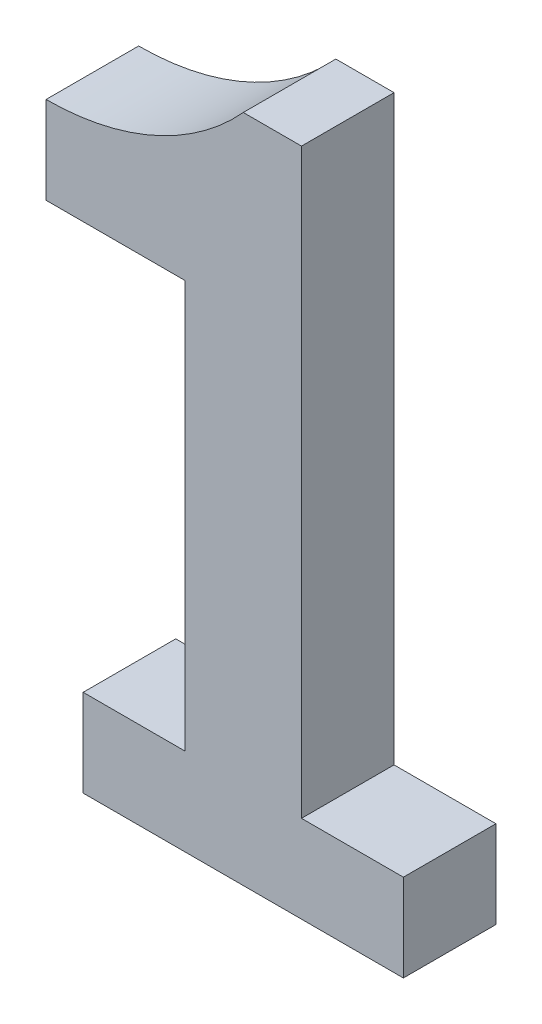
SolidWorks part; units mm, degrees
ref_plane "Front Plane" through (0, 0, 0) normal (0, 0, 1) x (1, 0, 0)
ref_plane "Top Plane" through (0, 0, 0) normal (0, 1, 0) x (1, 0, 0)
ref_plane "Right Plane" through (0, 0, 0) normal (1, 0, 0) x (0, 0, -1)
sketch "Sketch1" plane through (0, 0, 0) normal (0, 0, 1) x (1, 0, 0)
  line L1 (-76.2, 57.15) -> (76.2, 57.15)
  line L2 (-76.2, 57.15) -> (-76.2, -57.15)
  line L3 (-76.2, -57.15) -> (76.2, -57.15)
  line L4 (76.2, 57.15) -> (76.2, -57.15)
  line L5 (-76.2, 57.15) -> (76.2, -57.15) construction
  line L6 (-76.2, -57.15) -> (76.2, 57.15) construction
  point P0 (0, 0)
  dimension "D1" = 114.3
  dimension "D2" = 152.4
extrude "Boss-Extrude1" add sketch "Sketch1" along normal blind 3.18
sketch "Sketch2" plane through (0, 0, 3.18) normal (0, 0, 1) x (1, 0, 0)
  line L0 (48.0537, -28.069) -> (48.0537, -48.069)
  line L1 (48.0537, -48.069) -> (51.5537, -48.069)
  line L2 (51.5537, -48.069) -> (51.5537, -51.069)
  line L3 (51.5537, -51.069) -> (40.5537, -51.069)
  line L4 (40.5537, -51.069) -> (40.5537, -48.069)
  line L5 (40.5537, -48.069) -> (44.0537, -48.069)
  line L6 (44.0537, -48.069) -> (44.0537, -34.069)
  line L7 (44.0537, -34.069) -> (39.2788, -34.069)
  line L8 (39.2788, -34.069) -> (39.2788, -31.069)
  line L9 (48.0537, -28.069) -> (46.0537, -28.069)
  arc A0 (39.2788, -31.069) -> (46.0537, -28.069) centre (39.2788, -21.9191) ccw
extrude "Cut-Extrude2" cut sketch "Sketch2" against normal blind 3.18 flip side to cut
